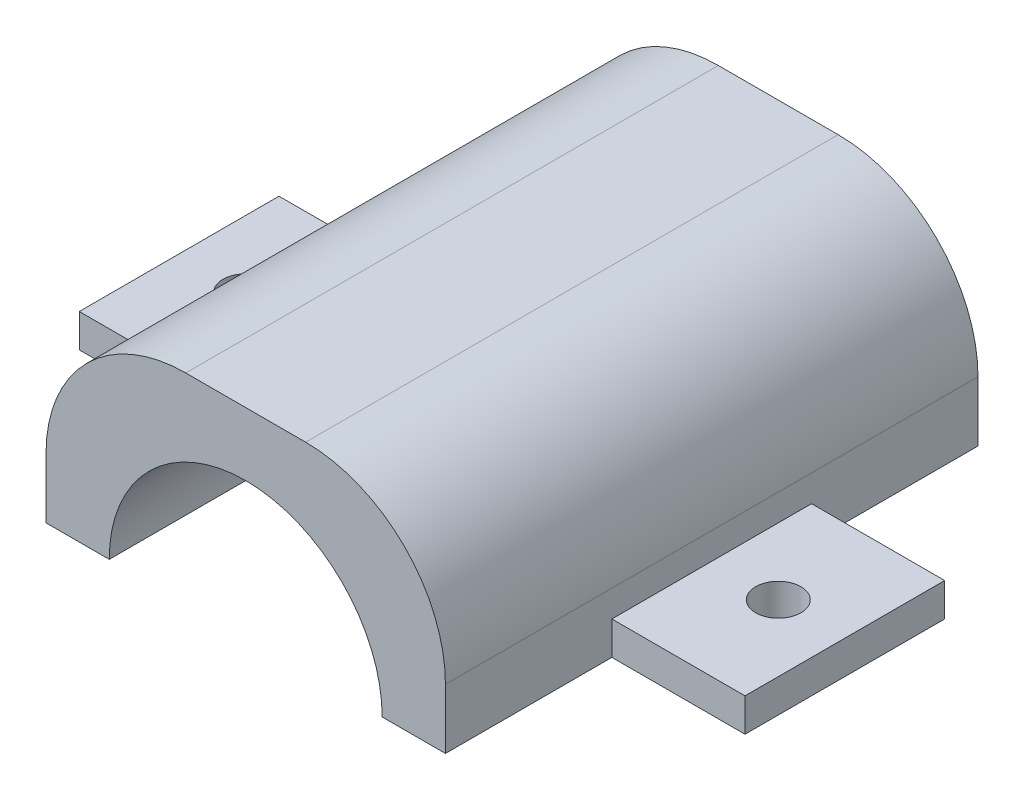
SolidWorks part; units mm, degrees
ref_plane "Front Plane" through (0, 0, 0) normal (0, 0, 1) x (1, 0, 0)
ref_plane "Top Plane" through (0, 0, 0) normal (0, 1, 0) x (1, 0, 0)
ref_plane "Right Plane" through (0, 0, 0) normal (1, 0, 0) x (0, 0, -1)
sketch "Sketch1" plane through (0, 0, 0) normal (0, 1, 0) x (1, 0, 0)
  line L1 (-14.6597, 19.3717) -> (15.3403, 19.3717)
  line L2 (-14.6597, 19.3717) -> (-14.6597, -20.6283)
  line L3 (-14.6597, -20.6283) -> (15.3403, -20.6283)
  line L4 (15.3403, 19.3717) -> (15.3403, -20.6283)
  dimension "D1" = 40
  dimension "D2" = 30
extrude "Boss-Extrude1" add sketch "Sketch1" along normal blind 15
sketch "Sketch2" plane through (0, 0, 20.6283) normal (0, 0, 1) x (1, 0, 0)
  line L0 (-14.6597, 0) -> (15.3403, 0) construction
  circle A0 centre (0.3403, 0) radius 10.25
  dimension "D1" = 20.5
extrude "Cut-Extrude1" cut sketch "Sketch2" against normal through all
sketch "Sketch3" plane through (0, 0, 0) normal (0, -1, 0) x (-1, 0, 0)
  line L0 (14.6597, 19.3717) -> (14.6597, -20.6283) construction
  line L1 (24.6597, 6.8717) -> (14.6597, 6.8717)
  line L2 (24.6597, 6.8717) -> (24.6597, -8.1283)
  line L3 (24.6597, -8.1283) -> (14.6597, -8.1283)
  line L4 (14.6597, 6.8717) -> (14.6597, -8.1283)
  point P6 (14.6597, -0.6283)
  point P7 (14.6597, -0.6283)
  dimension "D1" = 15
  dimension "D2" = 10
extrude "Boss-Extrude2" add sketch "Sketch3" against normal blind 2.5 separate body
sketch "Sketch4" plane through (0, 0, 0) normal (0, -1, 0) x (1, 0, 0)
  line L0 (15.3403, 20.6283) -> (15.3403, -19.3717) construction
  line L1 (15.3403, 8.1283) -> (25.3403, 8.1283)
  line L2 (15.3403, 8.1283) -> (15.3403, -6.8717)
  line L3 (15.3403, -6.8717) -> (25.3403, -6.8717)
  line L4 (25.3403, 8.1283) -> (25.3403, -6.8717)
  point P6 (15.3403, 0.6283)
  point P7 (15.3403, 0.6283)
  dimension "D1" = 10
  dimension "D2" = 15
extrude "Boss-Extrude3" add sketch "Sketch4" against normal blind 2.5
hole_wizard "M3 Clearance Hole1" positions "Sketch8" profile "Sketch6" hole size "M3" standard "ANSI Metric" end condition up to next
sketch "Sketch8" plane through (0, 0, 0) normal (0, -1, 0) x (-1, 0, 0)
  line L0 (-25.3403, 6.8717) -> (-25.3403, -8.1283) construction
  line L1 (-15.3403, 6.8717) -> (-25.3403, 6.8717) construction
  line L2 (14.6597, -8.1283) -> (24.6597, -8.1283) construction
  line L3 (24.6597, -8.1283) -> (24.6597, 6.8717) construction
  point P0 (-20.3403, -0.6283)
  point P2 (19.6597, -0.6283)
  point P7 (-25.3403, -0.6283)
  point P10 (-20.3403, 6.8717)
  point P13 (19.6597, -8.1283)
  point P16 (24.6597, -0.6283)
sketch "Sketch6" plane through (20.3403, 0, 0.6283) normal (1, 0, 0) x (0, 0, -1)
  line L0 (0, 0) -> (0, 2.501)
  line L1 (0, 2.501) -> (1.7, 2.501)
  line L2 (1.7, 2.501) -> (1.7, 0)
  line L5 (1.7, 0) -> (0, 0)
  line L11 (0, -6.35) -> (0, 107.95) construction
  dimension "Thru Hole Dia." = 3.4
  dimension "Thru Hole Depth" = 2.501
fillet "Fillet1" radius 10.5 2 edges at (15.3403, 15, 0.6283) (-14.6597, 15, 0.6283)
